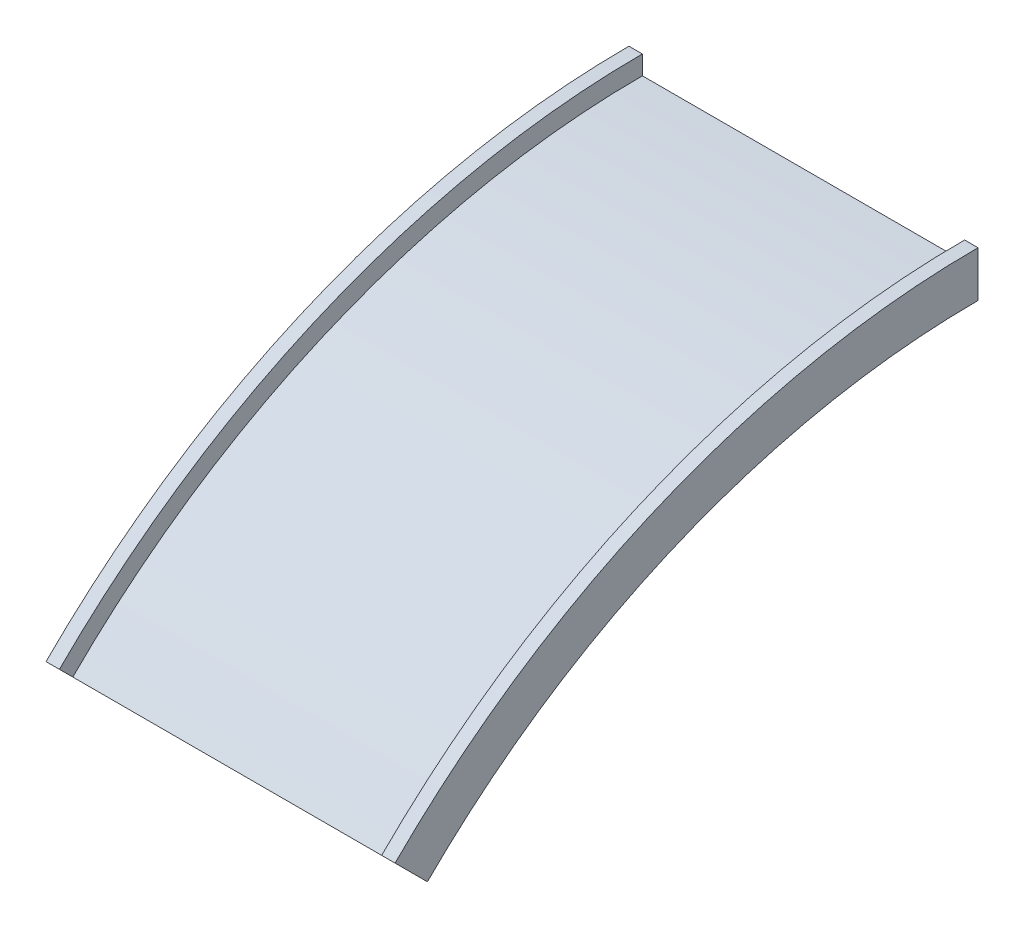
SolidWorks part; units mm, degrees
ref_plane "Front Plane" through (0, 0, 0) normal (0, 0, 1) x (1, 0, 0)
ref_plane "Top Plane" through (0, 0, 0) normal (0, 1, 0) x (1, 0, 0)
ref_plane "Right Plane" through (0, 0, 0) normal (1, 0, 0) x (0, 0, -1)
sketch "Sketch1" plane through (0, 0, 0) normal (0, 0, 1) x (1, 0, 0)
  line L0 (0, 0) -> (25, 0)
  line L1 (25, 0) -> (25, -35.2361)
  line L2 (25, -35.2361) -> (625, -35.2361)
  line L3 (625, -35.2361) -> (625, 0)
  line L4 (625, 0) -> (650, 0)
  line L5 (650, 0) -> (650, -85.2361)
  line L6 (650, -85.2361) -> (0, -85.2361)
  line L7 (0, -85.2361) -> (0, 0)
  line L8 (0, -1535.2361) -> (650, -1535.2361)
  dimension "D1" = 25
  dimension "D2" = 35.2361
  dimension "D3" = 650
  dimension "D4" = 50
  dimension "D5" = 1500
revolve "Revolve2" add sketch "Sketch1" angle 45 about L8
